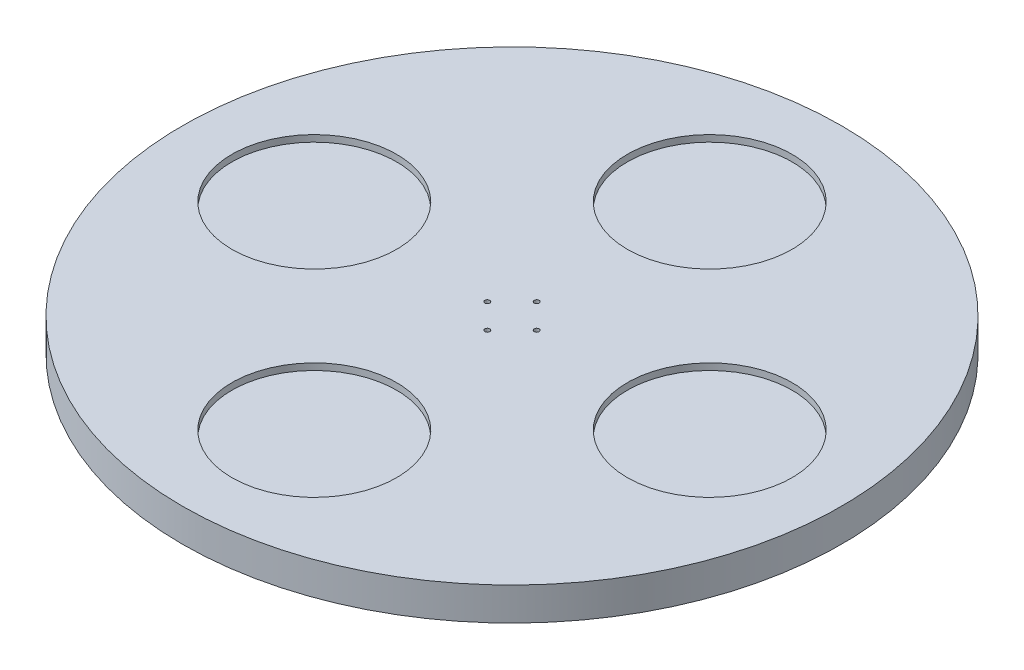
SolidWorks part; units mm, degrees
ref_plane "Alzado" through (0, 0, 0) normal (0, 0, 1) x (1, 0, 0)
ref_plane "Planta" through (0, 0, 0) normal (0, 1, 0) x (1, 0, 0)
ref_plane "Vista lateral" through (0, 0, 0) normal (1, 0, 0) x (0, 0, -1)
sketch "Croquis1" plane through (0, 0, 0) normal (0, 1, 0) x (1, 0, 0)
  circle A0 centre (0, 0) radius 100
  dimension "D1" = 200
extrude "Saliente-Extruir1" add sketch "Croquis1" along normal blind 10
sketch "Croquis2" plane through (0, 10, 0) normal (0, 1, 0) x (1, 0, 0)
  line L0 (0, 10) -> (0, -10) construction
  line L1 (-10, 0) -> (10, 0) construction
  circle A0 centre (0, 0) radius 10
  circle A1 centre (-7.5, 0) radius 0.75
  circle A2 centre (0, 7.5) radius 0.75
  circle A3 centre (7.5, 0) radius 0.75
  circle A4 centre (0, -7.5) radius 0.75
  point P18 (0, 0)
  dimension "D1" = 20
  dimension "D2" = 1.5
  dimension "D3" = 7.5
  dimension "D4" = 4
extrude "Cortar-Extruir1" cut sketch "Croquis2" against normal through all contours A1 | A4 | A3 | A2
sketch "Croquis3" plane through (0, 10, 0) normal (0, 1, 0) x (1, 0, 0)
  line L0 (0, 100) -> (0, -100) construction
  line L1 (-100, 0) -> (100, 0) construction
  circle A0 centre (0, 0) radius 100 construction
  circle A1 centre (-60, 0) radius 25
  circle A2 centre (0, 60) radius 25
  circle A3 centre (60, 0) radius 25
  circle A4 centre (0, -60) radius 25
  point P19 (0, 0)
  dimension "D1" = 50
  dimension "D2" = 60
  dimension "D3" = 4
extrude "Cortar-Extruir2" cut sketch "Croquis3" against normal blind 2
